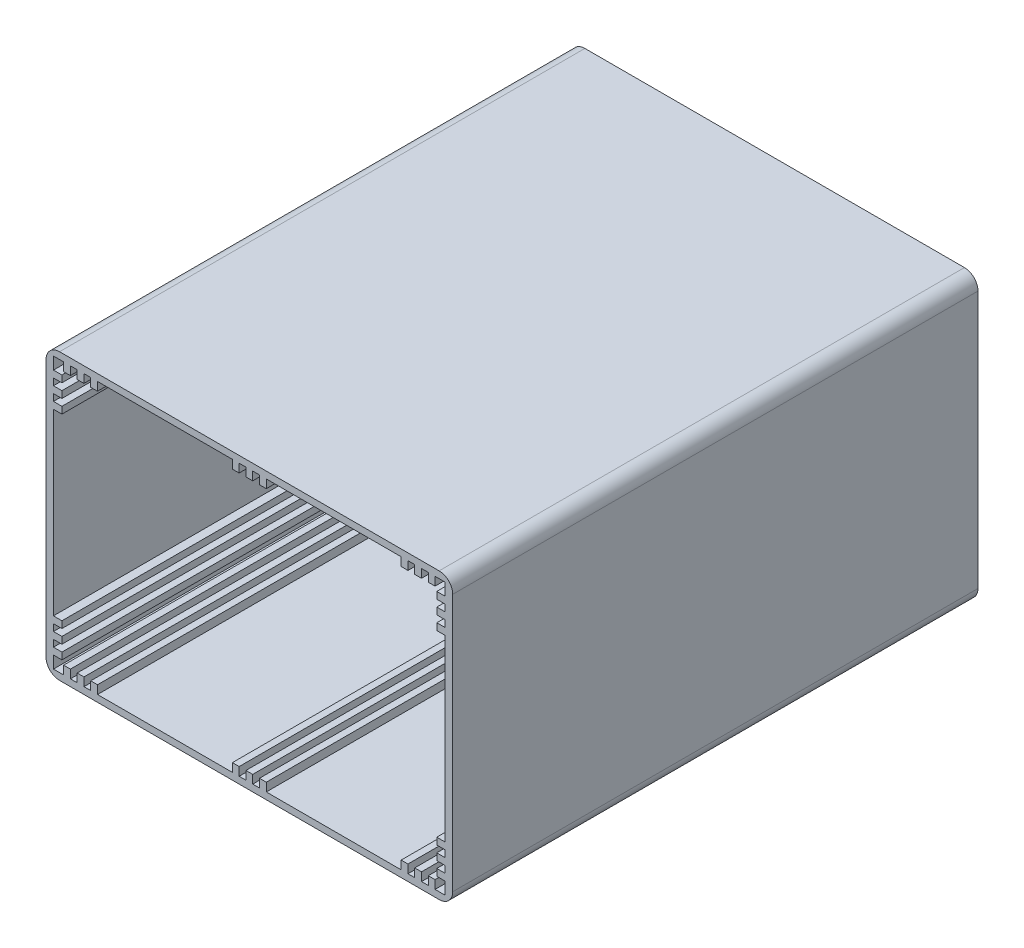
SolidWorks part; units mm, degrees
ref_plane "Front Plane" through (0, 0, 0) normal (0, 0, 1) x (1, 0, 0)
ref_plane "Top Plane" through (0, 0, 0) normal (0, 1, 0) x (1, 0, 0)
ref_plane "Right Plane" through (0, 0, 0) normal (1, 0, 0) x (0, 0, -1)
sketch "Sketch1" plane through (0, 0, 0) normal (0, 0, 1) x (1, 0, 0)
  line L1 (-60, -42) -> (60, -42)
  line L2 (-60, -42) -> (-60, 42)
  line L3 (-60, 42) -> (60, 42)
  line L4 (60, -42) -> (60, 42)
  line L5 (-60, -42) -> (60, 42) construction
  line L6 (-60, 42) -> (60, -42) construction
  line L7 (-57.8, -40) -> (57.8, -40)
  line L8 (-57.8, -40) -> (-57.8, 40)
  line L9 (-57.8, 40) -> (57.8, 40)
  line L10 (57.8, -40) -> (57.8, 40)
  line L11 (-57.8, -40) -> (57.8, 40) construction
  line L12 (-57.8, 40) -> (57.8, -40) construction
  point P0 (0, 0)
  point P6 (0, 0)
  dimension "D1" = 120
  dimension "D2" = 84
  dimension "D3" = 2
  dimension "D4" = 2.2
extrude "Boss-Extrude1" add sketch "Sketch1" along normal blind 155
fillet "Fillet1" radius 4 4 edges at (-60, -42, 77.5) (60, -42, 77.5) (60, 42, 77.5) (-60, 42, 77.5)
sketch "Sketch3" plane through (0, 0, 155) normal (0, 0, 1) x (1, 0, 0)
  line L0 (57.8, 40) -> (-57.8, 40) construction
  line L1 (-54.8, 40) -> (-52.8, 40)
  line L2 (-54.8, 40) -> (-54.8, 37.5)
  line L3 (-54.8, 37.5) -> (-52.8, 37.5)
  line L4 (-52.8, 40) -> (-52.8, 37.5)
  line L5 (-60, 38) -> (-60, -38) construction
  line L6 (-50.8, 40) -> (-48.8, 40)
  line L7 (-50.8, 40) -> (-50.8, 37.5)
  line L8 (-50.8, 37.5) -> (-48.8, 37.5)
  line L9 (-48.8, 40) -> (-48.8, 37.5)
  line L10 (-46.8, 40) -> (-44.8, 40)
  line L11 (-46.8, 40) -> (-46.8, 37.5)
  line L12 (-46.8, 37.5) -> (-44.8, 37.5)
  line L13 (-44.8, 40) -> (-44.8, 37.5)
  line L14 (-57.8, 40) -> (-57.8, -40) construction
  line L15 (-57.8, 36.4) -> (-55.3, 36.4)
  line L16 (-57.8, 36.4) -> (-57.8, 34.4)
  line L17 (-57.8, 34.4) -> (-55.3, 34.4)
  line L18 (-55.3, 36.4) -> (-55.3, 34.4)
  line L19 (56, 42) -> (-56, 42) construction
  line L20 (-57.8, 32.4) -> (-55.3, 32.4)
  line L21 (-57.8, 32.4) -> (-57.8, 30.4)
  line L22 (-57.8, 30.4) -> (-55.3, 30.4)
  line L23 (-55.3, 32.4) -> (-55.3, 30.4)
  line L24 (-57.8, 28.4) -> (-55.3, 28.4)
  line L25 (-57.8, 28.4) -> (-57.8, 26.4)
  line L26 (-57.8, 26.4) -> (-55.3, 26.4)
  line L27 (-55.3, 28.4) -> (-55.3, 26.4)
  line L28 (0, 40) -> (0, -40) construction
  line L29 (-57.8, -40) -> (57.8, -40) construction
  line L30 (-57.8, 0) -> (57.8, 0) construction
  line L31 (57.8, -40) -> (57.8, 40) construction
  line L32 (57.8, 26.4) -> (55.3, 26.4)
  line L33 (55.3, 28.4) -> (55.3, 26.4)
  line L34 (57.8, 28.4) -> (55.3, 28.4)
  line L35 (57.8, 28.4) -> (57.8, 26.4)
  line L36 (57.8, 30.4) -> (55.3, 30.4)
  line L37 (55.3, 32.4) -> (55.3, 30.4)
  line L38 (57.8, 32.4) -> (55.3, 32.4)
  line L39 (57.8, 32.4) -> (57.8, 30.4)
  line L40 (57.8, 34.4) -> (55.3, 34.4)
  line L41 (55.3, 36.4) -> (55.3, 34.4)
  line L42 (57.8, 36.4) -> (55.3, 36.4)
  line L43 (57.8, 36.4) -> (57.8, 34.4)
  line L44 (54.8, 37.5) -> (52.8, 37.5)
  line L45 (52.8, 40) -> (52.8, 37.5)
  line L46 (54.8, 40) -> (52.8, 40)
  line L47 (54.8, 40) -> (54.8, 37.5)
  line L48 (50.8, 37.5) -> (48.8, 37.5)
  line L49 (48.8, 40) -> (48.8, 37.5)
  line L50 (50.8, 40) -> (48.8, 40)
  line L51 (50.8, 40) -> (50.8, 37.5)
  line L52 (46.8, 37.5) -> (44.8, 37.5)
  line L53 (44.8, 40) -> (44.8, 37.5)
  line L54 (46.8, 40) -> (44.8, 40)
  line L55 (46.8, 40) -> (46.8, 37.5)
  line L56 (46.8, -40) -> (46.8, -37.5)
  line L57 (46.8, -40) -> (44.8, -40)
  line L58 (44.8, -40) -> (44.8, -37.5)
  line L59 (46.8, -37.5) -> (44.8, -37.5)
  line L60 (50.8, -40) -> (50.8, -37.5)
  line L61 (50.8, -40) -> (48.8, -40)
  line L62 (48.8, -40) -> (48.8, -37.5)
  line L63 (50.8, -37.5) -> (48.8, -37.5)
  line L64 (54.8, -40) -> (54.8, -37.5)
  line L65 (54.8, -40) -> (52.8, -40)
  line L66 (52.8, -40) -> (52.8, -37.5)
  line L67 (54.8, -37.5) -> (52.8, -37.5)
  line L68 (57.8, -36.4) -> (57.8, -34.4)
  line L69 (57.8, -36.4) -> (55.3, -36.4)
  line L70 (55.3, -36.4) -> (55.3, -34.4)
  line L71 (57.8, -34.4) -> (55.3, -34.4)
  line L72 (57.8, -32.4) -> (57.8, -30.4)
  line L73 (57.8, -32.4) -> (55.3, -32.4)
  line L74 (55.3, -32.4) -> (55.3, -30.4)
  line L75 (57.8, -30.4) -> (55.3, -30.4)
  line L76 (57.8, -28.4) -> (57.8, -26.4)
  line L77 (57.8, -28.4) -> (55.3, -28.4)
  line L78 (55.3, -28.4) -> (55.3, -26.4)
  line L79 (57.8, -26.4) -> (55.3, -26.4)
  line L80 (-46.8, -37.5) -> (-44.8, -37.5)
  line L81 (-44.8, -40) -> (-44.8, -37.5)
  line L82 (-46.8, -40) -> (-44.8, -40)
  line L83 (-46.8, -40) -> (-46.8, -37.5)
  line L84 (-50.8, -37.5) -> (-48.8, -37.5)
  line L85 (-48.8, -40) -> (-48.8, -37.5)
  line L86 (-50.8, -40) -> (-48.8, -40)
  line L87 (-50.8, -40) -> (-50.8, -37.5)
  line L88 (-54.8, -37.5) -> (-52.8, -37.5)
  line L89 (-52.8, -40) -> (-52.8, -37.5)
  line L90 (-54.8, -40) -> (-52.8, -40)
  line L91 (-54.8, -40) -> (-54.8, -37.5)
  line L92 (-57.8, -34.4) -> (-55.3, -34.4)
  line L93 (-55.3, -36.4) -> (-55.3, -34.4)
  line L94 (-57.8, -36.4) -> (-55.3, -36.4)
  line L95 (-57.8, -36.4) -> (-57.8, -34.4)
  line L96 (-57.8, -30.4) -> (-55.3, -30.4)
  line L97 (-55.3, -32.4) -> (-55.3, -30.4)
  line L98 (-57.8, -32.4) -> (-55.3, -32.4)
  line L99 (-57.8, -32.4) -> (-57.8, -30.4)
  line L100 (-57.8, -26.4) -> (-55.3, -26.4)
  line L101 (-55.3, -28.4) -> (-55.3, -26.4)
  line L102 (-57.8, -28.4) -> (-55.3, -28.4)
  line L103 (-57.8, -28.4) -> (-57.8, -26.4)
  line L104 (-5, -37.5) -> (-3, -37.5)
  line L105 (-5, 40) -> (-3, 40)
  line L106 (-5, 40) -> (-5, 37.5)
  line L107 (-5, 37.5) -> (-3, 37.5)
  line L108 (-3, 40) -> (-3, 37.5)
  line L109 (-1, 40) -> (1, 40)
  line L110 (-1, 40) -> (-1, 37.5)
  line L111 (-1, 37.5) -> (1, 37.5)
  line L112 (1, 40) -> (1, 37.5)
  line L113 (3, 40) -> (5, 40)
  line L114 (3, 40) -> (3, 37.5)
  line L115 (3, 37.5) -> (5, 37.5)
  line L116 (5, 40) -> (5, 37.5)
  line L117 (-3, -40) -> (-3, -37.5)
  line L118 (-5, -40) -> (-3, -40)
  line L119 (-5, -40) -> (-5, -37.5)
  line L120 (-1, -37.5) -> (1, -37.5)
  line L121 (1, -40) -> (1, -37.5)
  line L122 (-1, -40) -> (1, -40)
  line L123 (-1, -40) -> (-1, -37.5)
  line L124 (3, -37.5) -> (5, -37.5)
  line L125 (5, -40) -> (5, -37.5)
  line L126 (3, -40) -> (5, -40)
  line L127 (3, -40) -> (3, -37.5)
  point P124 (0, 37.5)
  point P125 (3, 38.75)
  dimension "D1" = 2
  dimension "D2" = 2.5
  dimension "D3" = 2
  dimension "D4" = 2
  dimension "D5" = 15.2
  dimension "D6" = 2
  dimension "D7" = 2.5
  dimension "D8" = 2
  dimension "D9" = 2
  dimension "D10" = 15.6
  dimension "D11" = 2
  dimension "D12" = 2
  dimension "D13" = 2
  dimension "D14" = 2.5
extrude "FinalBox" add sketch "Sketch3" against normal through all
